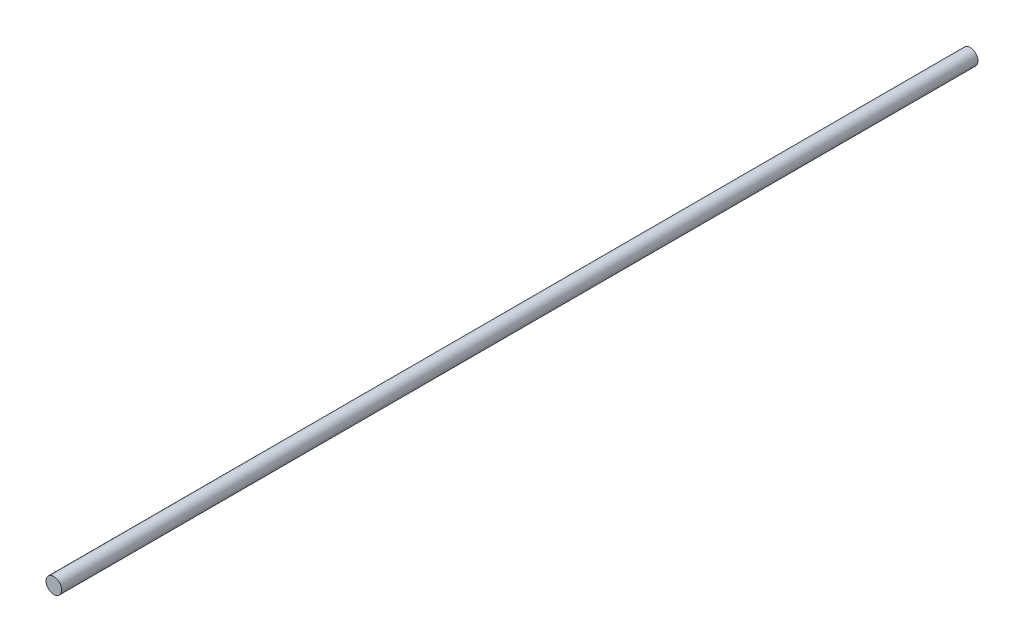
SolidWorks part; units mm, degrees
ref_plane "前视基准面" through (0, 0, 0) normal (0, 0, 1) x (1, 0, 0)
ref_plane "上视基准面" through (0, 0, 0) normal (0, 1, 0) x (1, 0, 0)
ref_plane "右视基准面" through (0, 0, 0) normal (1, 0, 0) x (0, 0, -1)
other "Configuration Table"
sketch "草图1" plane through (0, 0, 0) normal (0, 0, 1) x (1, 0, 0)
  circle A0 centre (-1.3846, 4.5288) radius 1.45
  dimension "D1" = 2.9
extrude "凸台-拉伸1" add sketch "草图1" along normal blind 170
